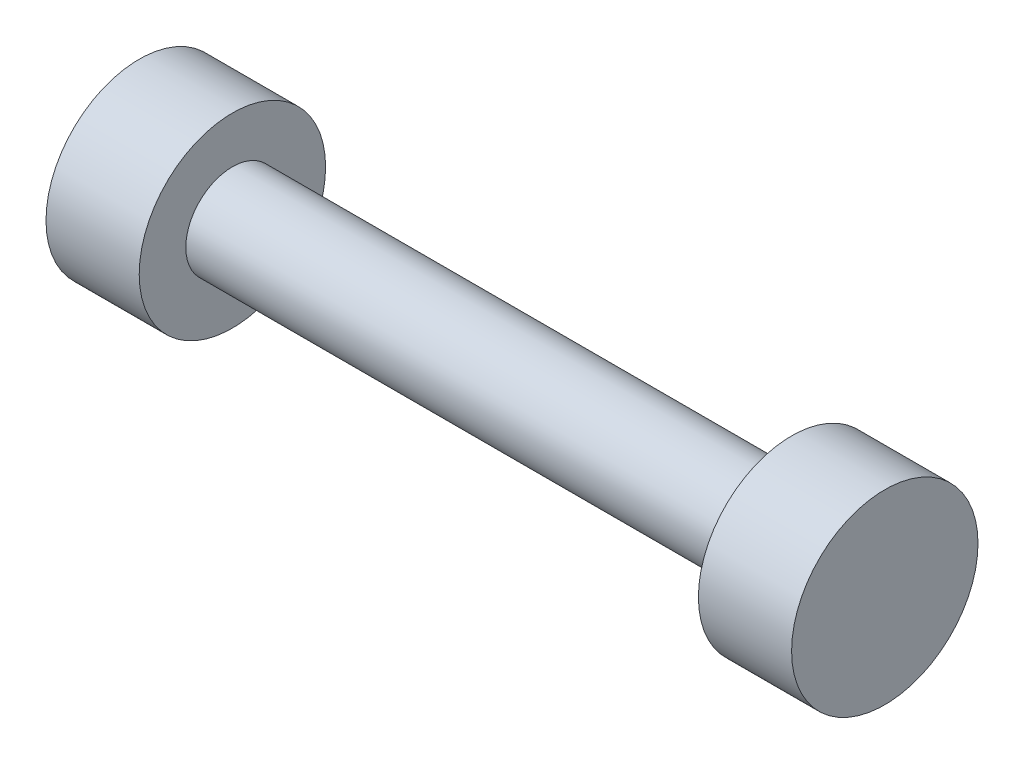
SolidWorks part; units mm, degrees
material "Hierro dúctil"
ref_plane "Alzado" through (0, 0, 0) normal (0, 0, 1) x (1, 0, 0)
ref_plane "Planta" through (0, 0, 0) normal (0, 1, 0) x (1, 0, 0)
ref_plane "Vista lateral" through (0, 0, 0) normal (1, 0, 0) x (0, 0, -1)
sketch "Croquis1" plane through (0, 0, 0) normal (0, 1, 0) x (1, 0, 0)
  line L0 (15, 2.5) -> (15, 5)
  line L3 (-15, 2.5) -> (15, 2.5)
  line L5 (0, 0) -> (15, 2.5) construction
  line L6 (-15, 2.5) -> (0, 0) construction
  line L9 (15, 5) -> (20, 5)
  line L10 (20, 0) -> (20, 5)
  line L11 (0, 5.8824) -> (0, -2.5) construction
  line L12 (-15, 2.5) -> (-15, 5)
  line L14 (-15, 5) -> (-20, 5)
  line L15 (-20, 0) -> (-20, 5)
  line L18 (-39.502, 0) -> (38.9357, 0) construction
  line L19 (-20, 0) -> (20, 0)
  point P0 (0, 0)
  point P6 (30, 0)
  dimension "D1" = 30
  dimension "D2" = 5
  dimension "D3" = 5
revolve "Revolución1" add sketch "Croquis1" angle 360 about L18
